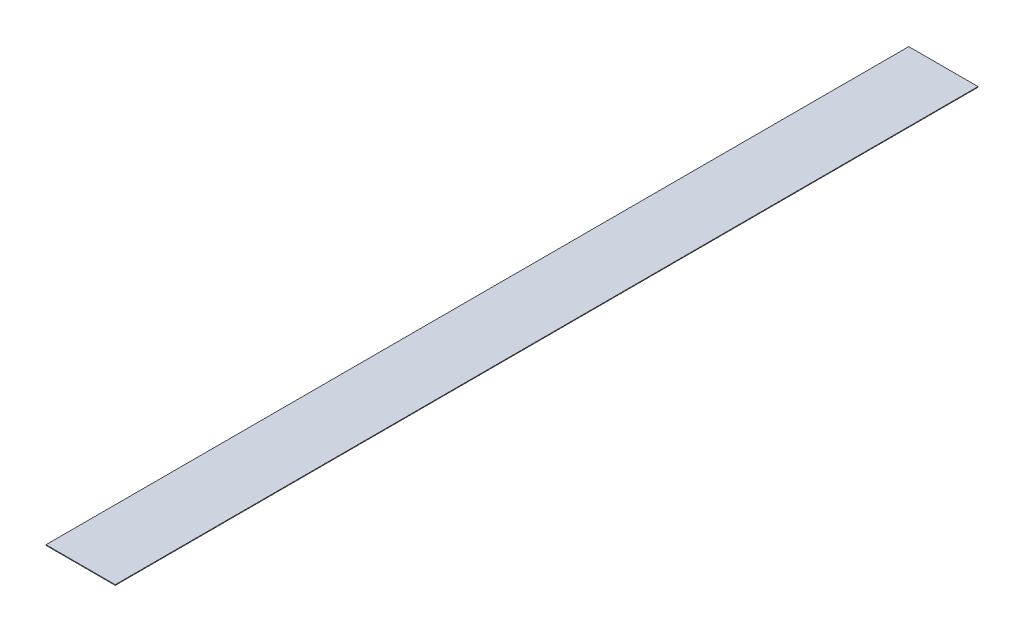
SolidWorks part; units mm, degrees
material "cable mix no adhesive"
ref_plane "Front" through (0, 0, 0) normal (0, 0, 1) x (1, 0, 0)
ref_plane "Top" through (0, 0, 0) normal (0, 1, 0) x (1, 0, 0)
ref_plane "Right" through (0, 0, 0) normal (1, 0, 0) x (0, 0, -1)
sketch "Sketch1" plane through (0, 0, 0) normal (0, 1, 0) x (1, 0, 0)
  line L0 (12.3027, 153.25) -> (-12.3027, -153.25) construction
  line L1 (-12.3027, 153.25) -> (12.3027, 153.25)
  line L2 (-12.3027, 153.25) -> (-12.3027, -153.25)
  line L3 (-12.3027, -153.25) -> (12.3027, -153.25)
  line L4 (12.3027, 153.25) -> (12.3027, -153.25)
  point P5 (0, 0)
  dimension "D1" = 24.6054
  dimension "D2" = 306.5
extrude "Extrude1" add sketch "Sketch1" along normal blind 0.22
